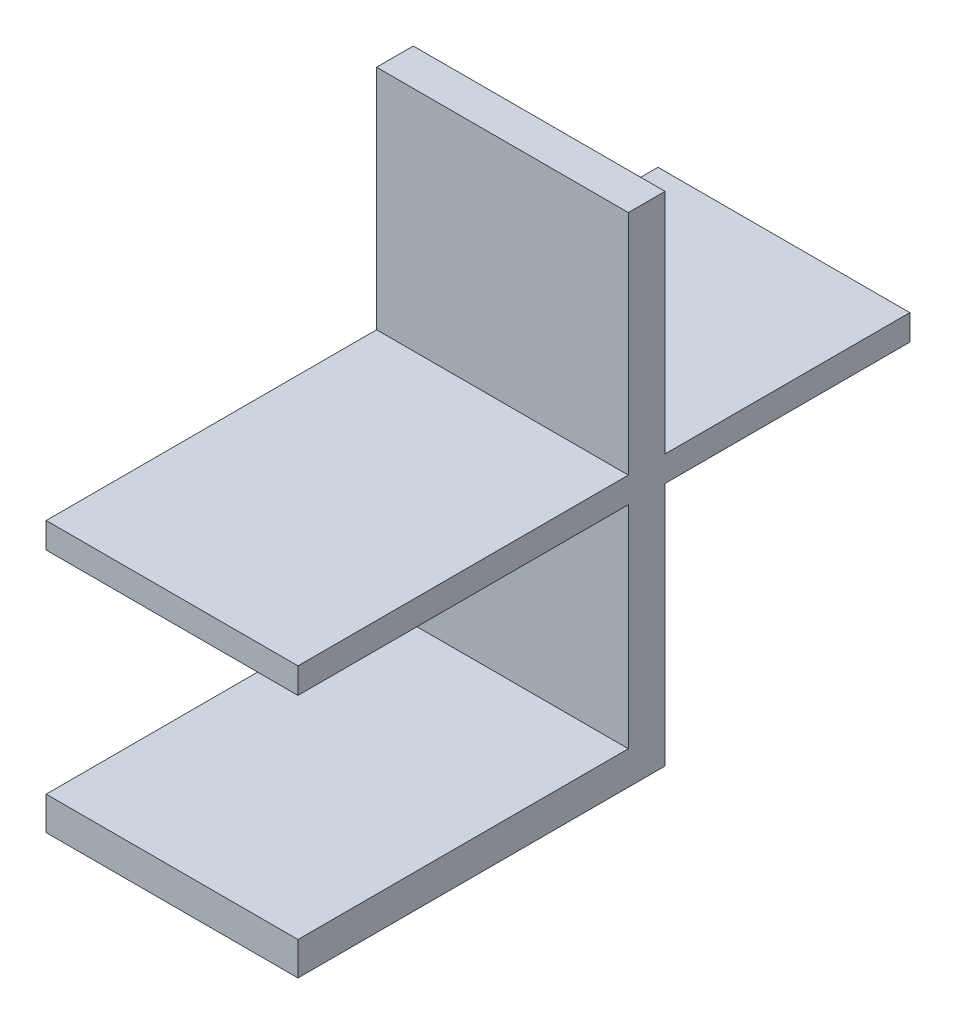
SolidWorks part; units mm, degrees
ref_plane "Front Plane" through (0, 0, 0) normal (0, 0, 1) x (1, 0, 0)
ref_plane "Top Plane" through (0, 0, 0) normal (0, 1, 0) x (1, 0, 0)
ref_plane "Right Plane" through (0, 0, 0) normal (1, 0, 0) x (0, 0, -1)
sketch "Sketch1" plane through (0, 0, 195.5672) normal (0, 0, 1) x (1, 0, 0)
  line L2 (110.9475, 27.6261) -> (90.3712, 27.6261)
  line L3 (-21.9751, 27.6261) -> (110.9475, 27.6261) construction
  line L4 (90.3712, 25.5357) -> (110.9475, 25.5357)
  line L7 (90.3712, 27.6261) -> (90.3712, 25.5357)
  line L8 (110.9475, 27.6261) -> (110.9475, 25.5357)
extrude "Boss-Extrude1" add sketch "Sketch1" along normal blind 30 and the other way blind 20
sketch "Sketch2" plane through (0, 0, 195.5672) normal (0, 0, 1) x (1, 0, 0)
  line L0 (110.9475, 46.208) -> (90.3712, 46.208)
  line L1 (90.3712, 27.6261) -> (90.3712, 46.208)
  line L2 (110.9475, 27.6261) -> (90.3712, 27.6261) construction
  line L4 (110.9475, 27.6261) -> (90.3712, 27.6261)
  line L6 (110.9475, 27.6261) -> (110.9475, 46.208)
extrude "Boss-Extrude2" add sketch "Sketch2" along normal blind 3
sketch "Sketch3" plane through (0, 25.5357, 0) normal (0, -1, 0) x (1, 0, 0)
  line L0 (110.9475, 198.5672) -> (110.9475, 195.5672)
  line L1 (90.3712, 198.5672) -> (110.9475, 198.5672)
  line L2 (90.3712, 198.5672) -> (90.3712, 195.5672)
  line L5 (110.9475, 175.5672) -> (110.9475, 225.5672) construction
  line L6 (110.9475, 195.5672) -> (90.3712, 195.5672)
extrude "Boss-Extrude3" add sketch "Sketch3" along normal blind 20
sketch "Sketch4" plane through (0, 0, 198.5672) normal (0, 0, 1) x (1, 0, 0)
  line L6 (90.3712, 5.5357) -> (90.3712, 25.5357) construction
  line L7 (110.9475, 5.5357) -> (90.3712, 5.5357)
  line L8 (110.9475, 5.5357) -> (110.9475, 8.2591)
  line L9 (110.9475, 8.2591) -> (90.3712, 8.2591)
  line L10 (90.3712, 5.5357) -> (90.3712, 8.2591)
extrude "Boss-Extrude4" add sketch "Sketch4" along normal blind 27
